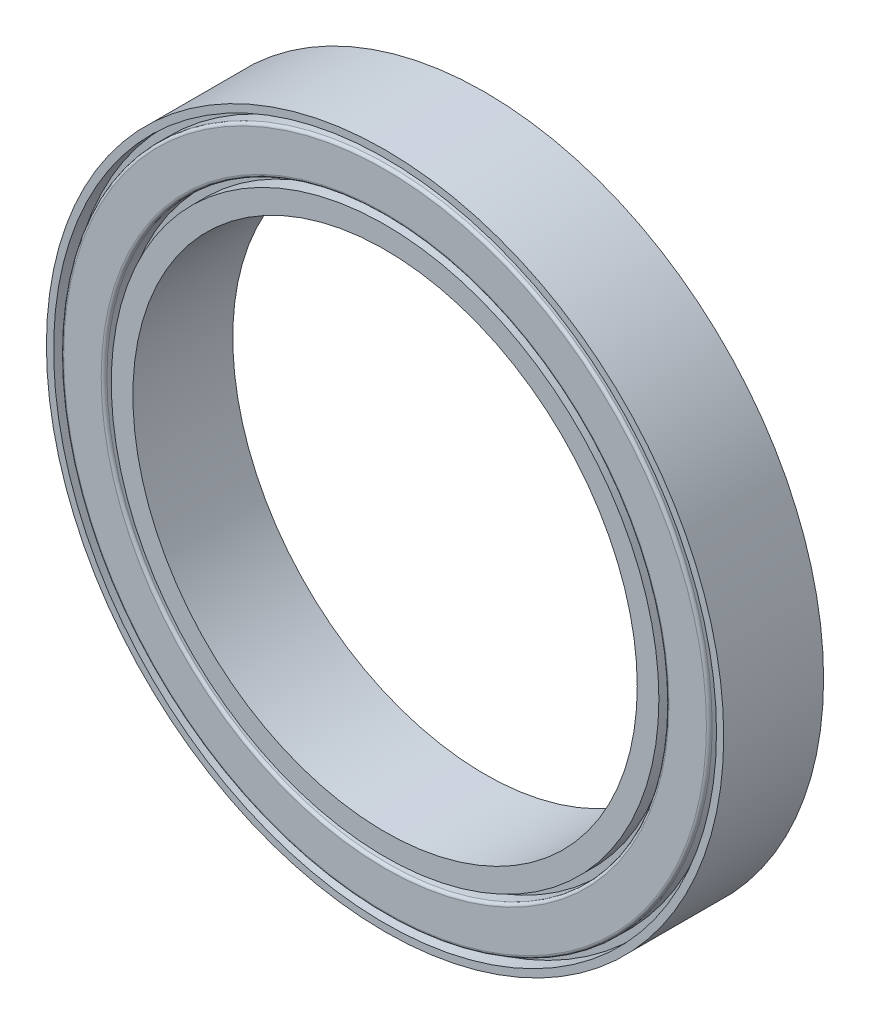
SolidWorks part; units mm, degrees
ref_plane "Front Plane" through (0, 0, 0) normal (0, 0, 1) x (1, 0, 0)
ref_plane "Top Plane" through (0, 0, 0) normal (0, 1, 0) x (1, 0, 0)
ref_plane "Right Plane" through (0, 0, 0) normal (1, 0, 0) x (0, 0, -1)
sketch "Sketch1" plane through (0, 0, 0) normal (0, 0, 1) x (1, 0, 0)
  circle A0 centre (0, 0) radius 23.5
  circle A1 centre (0, 0) radius 17.5
  dimension "D1" = 47
  dimension "D2" = 35
extrude "Boss-Extrude1" add sketch "Sketch1" along normal blind 6.93
sketch "Sketch2" plane through (0, 0, 6.93) normal (0, 0, 1) x (1, 0, 0)
  circle A0 centre (0, 0) radius 23
  circle A1 centre (0, 0) radius 22.5
  dimension "D1" = 45
  dimension "D2" = 46
extrude "Cut-Extrude1" cut sketch "Sketch2" against normal blind 1 contours A0 | A1
sketch "Sketch3" plane through (0, 0, 6.93) normal (0, 0, 1) x (1, 0, 0)
  circle A0 centre (0, 0) radius 19.5
  circle A1 centre (0, 0) radius 19
  dimension "D1" = 39
  dimension "D2" = 38
extrude "Cut-Extrude2" cut sketch "Sketch3" against normal blind 1
ref_plane "Plane1" through (0, 0, 3.465) normal (0, 0, 1) x (1, 0, 0)
mirror "Mirror1" about plane through (0, 0, 3.465) normal (0, 0, 1) of "Cut-Extrude1", "Cut-Extrude2"
fillet "Fillet1" radius 0.2 4 edges at (19.5, 0, 0) (22.5, 0, 0) (19.5, 0, 6.93) (22.5, 0, 6.93)
